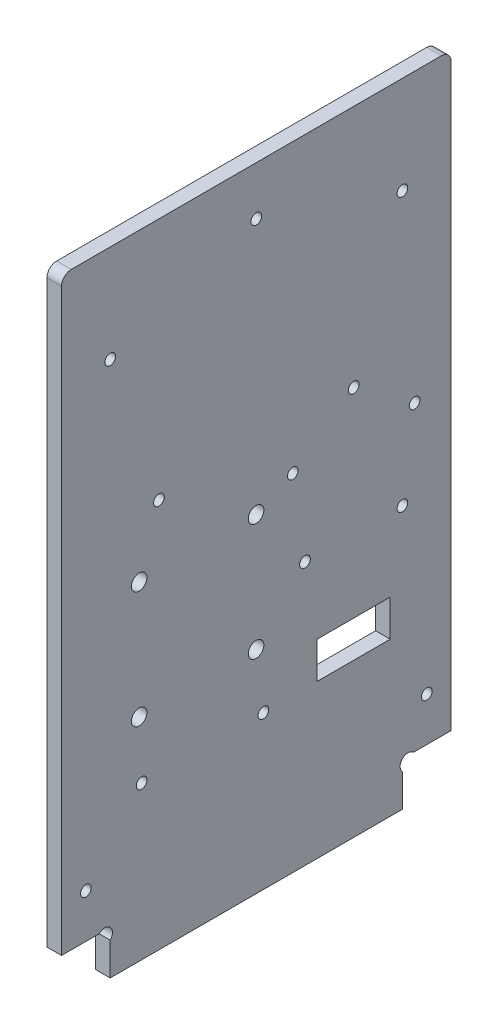
SolidWorks part; units mm, degrees
ref_plane "Plan de face" through (0, 0, 0) normal (0, 0, 1) x (1, 0, 0)
ref_plane "Plan de dessus" through (0, 0, 0) normal (0, 1, 0) x (1, 0, 0)
ref_plane "Plan de droite" through (0, 0, 0) normal (1, 0, 0) x (0, 0, -1)
sketch "Esquisse1" plane through (0, 0, 0) normal (1, 0, 0) x (0, 0, -1)
  line L8 (10, 6.7373) -> (10, 0)
  line L9 (70, 6.7373) -> (70, 0)
  line L10 (7.7373, 9) -> (0, 9)
  line L11 (10, 0) -> (70, 0)
  line L12 (72.2627, 9) -> (80, 9)
  line L13 (0, 9) -> (0, 130)
  line L14 (0, 130) -> (80, 130)
  line L15 (80, 130) -> (80, 9)
  arc A0 (10, 6.7373) -> (7.7373, 9) centre (8.8686, 7.8686) ccw
  arc A1 (70, 6.7373) -> (72.2627, 9) centre (71.1314, 7.8686) cw
  dimension "D7" = 1.1314
  dimension "D6" = 1.6
  dimension "D1" = 9
  dimension "D2" = 10
  dimension "D3" = 10
  dimension "D4" = 80
  dimension "D5" = 130
  dimension "D8" = 1.1314
  dimension "D9" = 1.1314
  dimension "D10" = 1.1314
extrude "Extrusion1" add sketch "Esquisse1" along normal blind 3
sketch "Esquisse2" plane through (3, 0, 0) normal (1, 0, 0) x (0, 0, -1)
  line L0 (0, 9) -> (7.7373, 9) construction
  line L1 (0, 130) -> (0, 9) construction
  line L2 (80, 9) -> (80, 130) construction
  line L3 (72.2627, 9) -> (80, 9) construction
  line L4 (80, 130) -> (0, 130) construction
  circle A0 centre (60, 80) radius 1.1
  circle A1 centre (10, 110) radius 1.1
  circle A2 centre (20, 80) radius 1.1
  circle A3 centre (70, 110) radius 1.1
  circle A4 centre (15.95, 67.45) radius 1.6
  circle A5 centre (15.95, 43.45) radius 1.6
  circle A6 centre (39.95, 43.45) radius 1.6
  circle A7 centre (39.95, 67.45) radius 1.6
  circle A8 centre (40, 120) radius 1.1
  circle A9 centre (70, 54) radius 1.1
  circle A10 centre (50, 54) radius 1.1
  dimension "D5" = 15.95
  dimension "D7" = 10
  dimension "D9" = 10
  dimension "D4" = 3.2
  dimension "D6" = 2.2
  dimension "D1" = 58.45
  dimension "D2" = 24
  dimension "D3" = 24
  dimension "D8" = 40
  dimension "D10" = 30
  dimension "D11" = 10
  dimension "D12" = 20
  dimension "D13" = 10
  dimension "D14" = 10
  dimension "D15" = 10
  dimension "D16" = 20
  dimension "D17" = 45
extrude "Enlèv. mat.-Extru.1" cut sketch "Esquisse2" against normal through all
sketch "Esquisse3" plane through (0, 0, 0) normal (-1, 0, 0) x (0, 0, 1)
  line L1 (-67.5, 39) -> (-52.5, 39)
  line L2 (-67.5, 39) -> (-67.5, 31.5)
  line L3 (-67.5, 31.5) -> (-52.5, 31.5)
  line L4 (-52.5, 39) -> (-52.5, 31.5)
  circle A0 centre (-70, 54) radius 1.1 construction
  circle A1 centre (-50, 54) radius 1.1 construction
  dimension "D4" = 2.5
  dimension "D1" = 15
  dimension "D2" = 7.5
  dimension "D3" = 15
  dimension "D5" = 2.5
extrude "Enlèv. mat.-Extru.2" cut sketch "Esquisse3" against normal through all
sketch "Esquisse4" plane through (3, 0, 0) normal (1, 0, 0) x (0, 0, -1)
  line L3 (0, 9) -> (7.7373, 9) construction
  line L4 (0, 130) -> (0, 9) construction
  line L5 (80, 9) -> (80, 130) construction
  circle A2 centre (75, 18) radius 1.1
  circle A3 centre (5, 18) radius 1.1
  dimension "D1" = 5
  dimension "D3" = 2.2
  dimension "D2" = 5
  dimension "D5" = 9
extrude "Enlèv. mat.-Extru.3" cut sketch "Esquisse4" against normal through all
fillet "Congé1" radius 2 2 edges at (1.5, 130, -80) (1.5, 130, 0)
sketch "Esquisse5" plane through (3, 0, 0) normal (1, 0, 0) x (0, 0, -1)
  line L0 (52.5, 31.5) -> (52.5, 39) construction
  line L1 (67.5, 39) -> (67.5, 31.5) construction
  circle A0 centre (16.45, 31.45) radius 1.1
  circle A1 centre (41.45, 31.45) radius 1.1
  circle A2 centre (47.5, 71) radius 1.1
  circle A3 centre (72.5, 71) radius 1.1
  circle A4 centre (15.95, 43.45) radius 1.6 construction
  circle A7 centre (50, 54) radius 1.1 construction
  dimension "D1" = 2.2
  dimension "D2" = 0.5
  dimension "D5" = 12
  dimension "D6" = 5
  dimension "D3" = 25
  dimension "D4" = 17
  dimension "D7" = 5
extrude "Enlèv. mat.-Extru.6" cut sketch "Esquisse5" against normal through all
